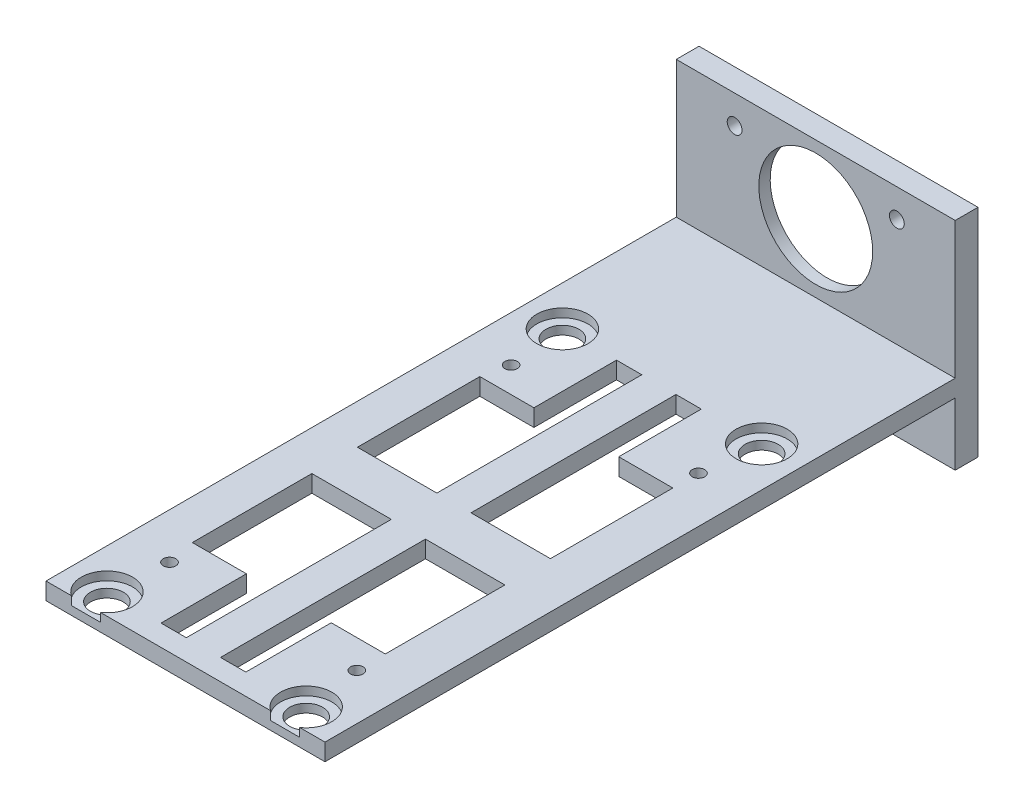
SolidWorks part; units mm, degrees
ref_plane "前视基准面" through (0, 0, 0) normal (0, 0, 1) x (1, 0, 0)
ref_plane "上视基准面" through (0, 0, 0) normal (0, 1, 0) x (1, 0, 0)
ref_plane "右视基准面" through (0, 0, 0) normal (1, 0, 0) x (0, 0, -1)
sketch "草图1" plane through (0, 0, 0) normal (0, 1, 0) x (1, 0, 0)
  line L0 (-35, 4) -> (-35, 25.5)
  line L1 (-1.1, 25.5) -> (-10.6, 25.5)
  line L2 (-10.6, 25.5) -> (-10.6, 40)
  line L3 (-21.05, 40) -> (-21.05, 4)
  line L4 (-1.1, 25.5) -> (-1.1, 4)
  line L5 (-1.1, -25) -> (-10.6, -25)
  line L6 (0, 40) -> (-1.1, 40)
  line L7 (-1.1, 40) -> (-1.1, 30) construction
  line L8 (-35, 40) -> (-34, 40)
  line L9 (-34, 40) -> (-34, 30) construction
  line L10 (-35, -40) -> (-34, -40)
  line L11 (-34, -40) -> (-34, -30) construction
  line L12 (0, -40) -> (-1.1, -40)
  line L13 (-1.1, -40) -> (-1.1, -30) construction
  line L14 (-10.6, -25) -> (-10.6, -40)
  line L15 (-21.05, 4) -> (-35, 4)
  line L16 (-1.1, -25) -> (-1.1, -4)
  line L17 (-42, 3.3) -> (-42, 50.3)
  line L18 (-42, 3.3) -> (-42, -43.7)
  line L19 (-42, -43.7) -> (0, -43.7)
  line L20 (0, -43.7) -> (7, -43.7)
  line L21 (-42, 50.3) -> (-42, 67)
  line L22 (7, -43.7) -> (7, 47)
  line L23 (-35, -4) -> (-35, -25)
  line L24 (-25.5, -25) -> (-35, -25)
  line L25 (-25.5, -40) -> (-25.5, -25)
  line L26 (-42, 67) -> (7, 67)
  line L27 (7, 67) -> (7, 47)
  line L29 (-15.05, 4) -> (-15.05, 40)
  line L30 (-25.5, 40) -> (-25.5, 25.5)
  line L32 (-25.5, 25.5) -> (-35, 25.5)
  line L33 (-21.05, 40) -> (-25.5, 40)
  line L34 (-15.05, 40) -> (-10.6, 40)
  line L35 (-15.05, 4) -> (-1.1, 4)
  line L36 (-21.05, -40) -> (-21.05, -4)
  line L37 (-21.05, -4) -> (-35, -4)
  line L38 (-25.5, -40) -> (-21.05, -40)
  line L39 (-15.05, -40) -> (-10.6, -40)
  line L40 (-15.05, -4) -> (-1.1, -4)
  line L41 (-15.05, -4) -> (-15.05, -40)
  circle A0 centre (-35, 40) radius 2.9
  circle A1 centre (0, 40) radius 2.9
  circle A2 centre (-35, -40) radius 2.9
  circle A3 centre (0, -40) radius 2.9
  circle A4 centre (-34, 30) radius 1.1
  circle A5 centre (-1.1, 30) radius 1.1
  circle A6 centre (-1.1, -30) radius 1.1
  circle A7 centre (-34, -30) radius 1.1
extrude "凸台-拉伸1" add sketch "草图1" along normal blind 3
sketch "草图2" plane through (0, 3, 0) normal (0, 1, 0) x (1, 0, 0)
  circle A0 centre (-35, 40) radius 4.5
  circle A1 centre (0, 40) radius 4.5
  circle A2 centre (0, -40) radius 4.5
  circle A3 centre (-35, -40) radius 4.5
extrude "切除-拉伸1" cut sketch "草图2" against normal blind 1.5
sketch "草图3" plane through (0, 3, 0) normal (0, 1, 0) x (1, 0, 0)
  line L0 (-42, 67) -> (-42, 71)
  line L1 (7, 67) -> (7, 71)
  line L2 (7, 71) -> (-42, 71)
  line L3 (-42, 67) -> (7, 67)
extrude "凸台-拉伸2" add sketch "草图3" along normal blind 24 and the other way blind 14
sketch "草图4" plane through (0, 0, -67) normal (0, 0, 1) x (1, 0, 0)
  line L0 (-17.5, 27) -> (-3.25, 27) construction
  line L1 (-42, 27) -> (7, 27) construction
  line L2 (-3.25, 27) -> (-3.25, 22) construction
  line L3 (-17.5, 27) -> (-31.75, 27) construction
  line L4 (-31.75, 27) -> (-31.75, 22) construction
  line L5 (-17.5, 27) -> (-17.5, 15)
  line L6 (-28.95, -9.5) -> (-28.95, -1.5)
  line L7 (-32.25, -6.5) -> (-32.25, -9.5) construction
  line L8 (-32.25, -6.5) -> (-32.25, -1.5) construction
  line L9 (-28.95, -1.5) -> (-6.95, -1.5)
  line L10 (-6.95, -1.5) -> (-6.95, -9.5)
  line L11 (-6.95, -9.5) -> (-28.95, -9.5)
  circle A0 centre (-31.75, 22) radius 1.3
  circle A1 centre (-3.25, 22) radius 1.3
  circle A2 centre (-2.75, -6.5) radius 1.3
  circle A3 centre (-32.25, -6.5) radius 1.3
  circle A4 centre (-17.5, 15) radius 10
  point P17 (0, 0)
extrude "切除-拉伸7" cut sketch "草图4" against normal through all
sketch "草图5" plane through (0, 0, -71) normal (0, 0, -1) x (-1, 0, 0)
  line L0 (2.1136, 22.6313) -> (2.1136, 23.2703)
  line L1 (2.1136, 23.2703) -> (32.0262, 23.2703)
  line L2 (32.0262, 23.2703) -> (33.611, 23.2703)
  line L3 (33.611, 23.2703) -> (33.611, -7.8243)
  line L4 (33.611, -7.8243) -> (2.1136, -7.8243)
  line L5 (2.1136, -7.8243) -> (2.1136, 22.6313)
  circle A0 centre (3.25, 22) radius 1.3 construction
  circle A1 centre (31.75, 22) radius 1.3 construction
extrude "切除-拉伸8" cut sketch "草图5" against normal blind 2
